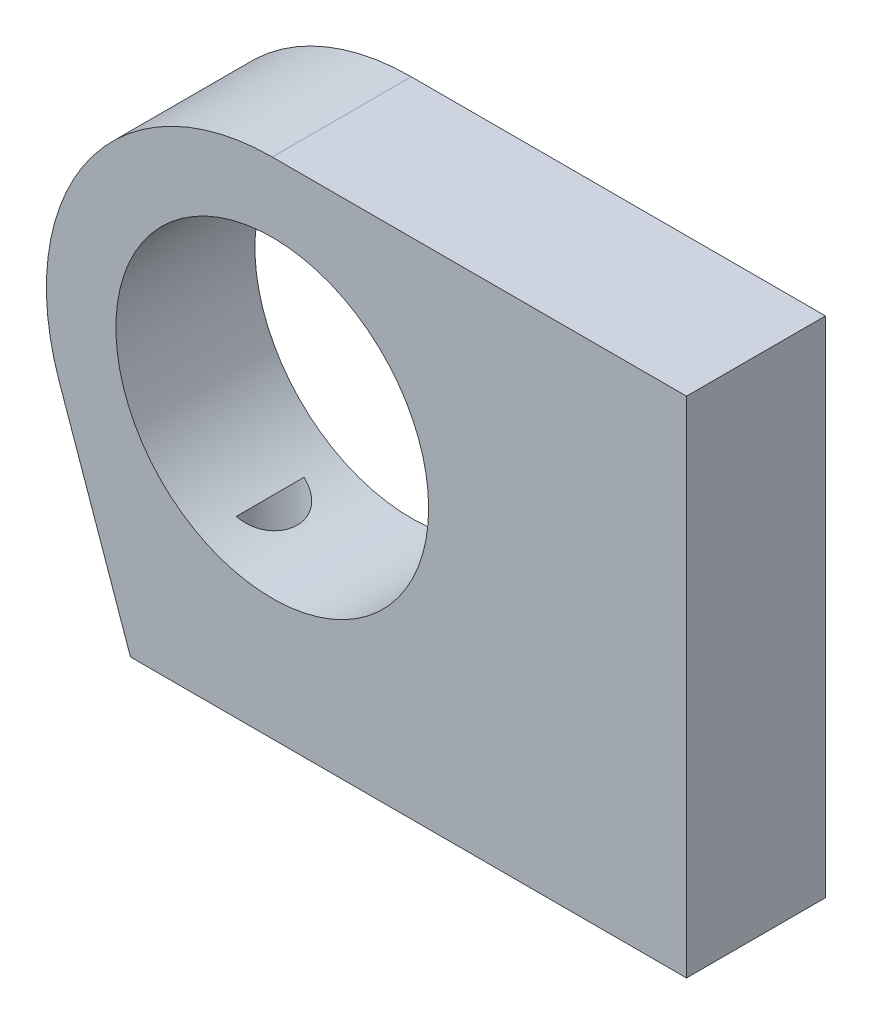
SolidWorks part; units mm, degrees
ref_plane "Front" through (0, 0, 0) normal (0, 0, 1) x (1, 0, 0)
ref_plane "Top" through (0, 0, 0) normal (0, 1, 0) x (1, 0, 0)
ref_plane "Right" through (0, 0, 0) normal (1, 0, 0) x (0, 0, -1)
sketch "Sketch1" plane through (0, 0, 0) normal (0, 0, 1) x (1, 0, 0)
  line L0 (0, 0) -> (50.8, 0)
  line L5 (0, 0) -> (-6.518, 18.5627)
  line L6 (50.8, 0) -> (50.8, 46.0375)
  line L7 (50.8, 46.0375) -> (12.954, 46.0375)
  circle A0 centre (12.954, 25.4) radius 6.35
  circle A1 centre (12.954, 25.4) radius 14.2875
  circle A2 centre (12.954, 25.4) radius 20.6375
  point P11 (12.954, 46.0375)
  point P13 (19.1795, 46.0375)
  dimension "D2" = 12.7
  dimension "D5" = 28.575
  dimension "D1" = 50.8
  dimension "D3" = 25.4
  dimension "D4" = 37.846
  dimension "D6" = 6.35
extrude "Boss-Extrude2" add sketch "Sketch1" along normal blind 12.7
sketch "Sketch2" plane through (0, 0, 0) normal (0, -1, 0) x (1, 0, 0)
  line L0 (0, 6.35) -> (50.8, 6.35) construction
  line L1 (0, 12.7) -> (0, 0) construction
  line L3 (50.8, 12.7) -> (50.8, 0) construction
  circle A0 centre (45.085, 6.35) radius 3.175
  circle A1 centre (5.715, 6.35) radius 3.175
  point P10 (50.8, 6.35)
  dimension "D3" = 6.35
  dimension "D1" = 5.715
  dimension "D2" = 5.715
extrude "Cut-Extrude1" cut sketch "Sketch2" against normal blind 12.7
ref_plane "Plane1" through (0, 46.0375, 0) normal (0, 1, 0) x (1, 0, 0)
equation "\"D2@Sketch2\"=\"D1@Sketch2\""
